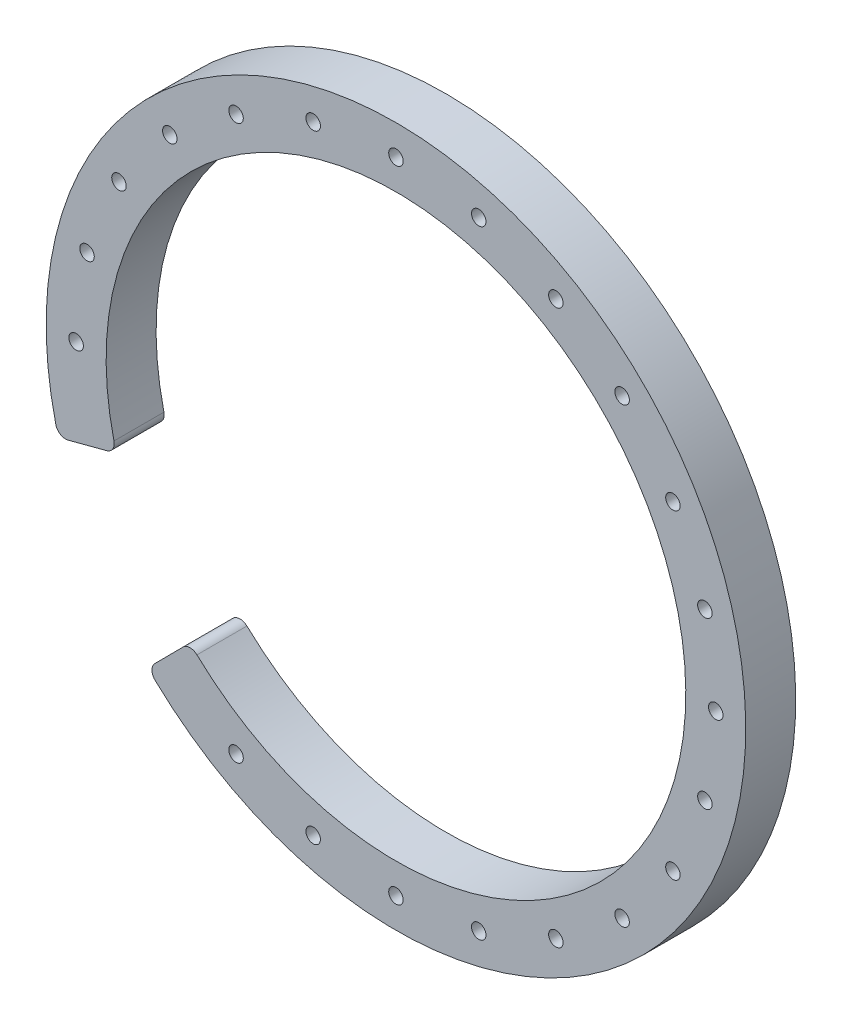
SolidWorks part; units mm, degrees
ref_plane "Front Plane" through (0, 0, 0) normal (0, 0, 1) x (1, 0, 0)
ref_plane "Top Plane" through (0, 0, 0) normal (0, 1, 0) x (1, 0, 0)
ref_plane "Right Plane" through (0, 0, 0) normal (1, 0, 0) x (0, 0, -1)
sketch "Sketch1" plane through (0, 0, 0) normal (0, 0, 1) x (1, 0, 0)
  line L0 (-13.2179, 0.4111) -> (-17.1056, -0.6154)
  line L1 (-17.1056, -0.6154) -> (-20.955, -1.6317)
  line L2 (2.0308, -26.0005) -> (-0.8019, -28.8541)
  line L3 (-0.8019, -28.8541) -> (-3.6068, -31.6796)
  arc A0 (-3.5649, -34.5386) -> (-23.41, -0.1659) centre (44.6471, 16.2117) ccw
  arc A1 (4.8234, -25.9555) -> (-11.7826, 2.807) centre (44.6471, 16.2117) ccw
  arc A2 (-20.955, -1.6317) -> (-23.41, -0.1659) centre (-21.4655, 0.302) cw
  arc A3 (4.8234, -25.9555) -> (2.0308, -26.0005) centre (3.4502, -27.4096) ccw
  arc A4 (-3.6068, -31.6796) -> (-3.5649, -34.5386) centre (-2.1874, -33.0886) ccw
  arc A5 (-11.7826, 2.807) -> (-13.2179, 0.4111) centre (-13.7285, 2.3448) cw
  circle A6 centre (-17.1721, 32.7761) radius 1.45
  circle A7 centre (-10.7785, 48.2117) radius 1.45
  circle A8 centre (-19.3529, 16.2117) radius 1.45
  circle A14 centre (106.4664, -0.3527) radius 1.45
  circle A15 centre (100.0727, -15.7883) radius 1.45
  circle A16 centre (89.9019, -29.0431) radius 1.45
  circle A17 centre (76.6471, -39.2139) radius 1.45
  circle A18 centre (61.2115, -45.6075) radius 1.45
  circle A19 centre (44.6471, -47.7883) radius 1.45
  circle A20 centre (28.0827, -45.6075) radius 1.45
  circle A21 centre (12.6471, -39.2139) radius 1.45
  circle A34 centre (-0.6077, 61.4666) radius 1.45
  circle A35 centre (12.6471, 71.6373) radius 1.45
  circle A36 centre (28.0827, 78.031) radius 1.45
  circle A37 centre (44.6471, 80.2117) radius 1.45
  circle A38 centre (61.2115, 78.031) radius 1.45
  circle A39 centre (76.6471, 71.6373) radius 1.45
  circle A40 centre (89.9019, 61.4666) radius 1.45
  circle A41 centre (100.0727, 48.2117) radius 1.45
  circle A42 centre (106.4664, 32.7761) radius 1.45
  circle A44 centre (108.6471, 16.2117) radius 1.45
  dimension "D1" = 2
  dimension "D2" = 2
  dimension "D3" = 70
  dimension "D4" = 12
  dimension "D5" = 64
  dimension "D7" = 64
  dimension "D9" = 64
  dimension "D6" = 64
  dimension "D8" = 64
  dimension "D10" = 64
  dimension "D11" = 64
  dimension "D12" = 64
  dimension "D13" = 64
  dimension "D14" = 64
  dimension "D15" = 64
  dimension "D16" = 64
  dimension "D17" = 64
  dimension "D18" = 64
  dimension "D19" = 64
  dimension "D20" = 64
  dimension "D21" = 64
  dimension "D22" = 64
  dimension "D23" = 64
  dimension "D24" = 64
  dimension "D25" = 64
extrude "Boss-Extrude1" add sketch "Sketch1" along normal blind 10
